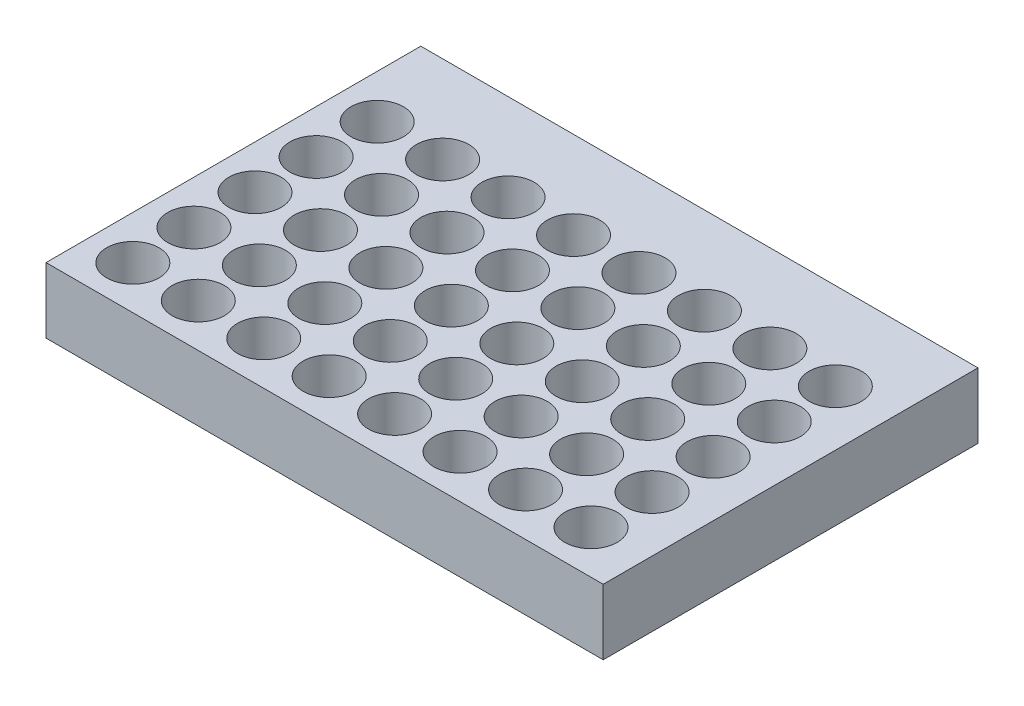
SolidWorks part; units mm, degrees
ref_plane "Front Plane" through (0, 0, 0) normal (0, 0, 1) x (1, 0, 0)
ref_plane "Top Plane" through (0, 0, 0) normal (0, 1, 0) x (1, 0, 0)
ref_plane "Right Plane" through (0, 0, 0) normal (1, 0, 0) x (0, 0, -1)
other "Graphic1"
sketch "Sketch1" plane through (0, 0, 0) normal (0, 1, 0) x (1, 0, 0)
  line L1 (-312.706, 132.0167) -> (-185.006, 132.0167)
  line L2 (-312.706, 132.0167) -> (-312.706, 46.1167)
  line L3 (-312.706, 46.1167) -> (-185.006, 46.1167)
  line L4 (-185.006, 132.0167) -> (-185.006, 46.1167)
  dimension "D1" = 85.9
  dimension "D2" = 127.7
extrude "Boss-Extrude1" add sketch "Sketch1" along normal blind 15
sketch "Sketch2" plane through (0, 15, 0) normal (0, 1, 0) x (1, 0, 0)
  line L0 (-185.006, 132.0167) -> (-312.706, 132.0167) construction
  line L1 (-312.706, 132.0167) -> (-312.706, 46.1167) construction
  circle A0 centre (-302.706, 112.0167) radius 6
  dimension "D1" = 20
  dimension "D3" = 12
  dimension "D2" = 10
extrude "Cut-Extrude1" cut sketch "Sketch2" against normal blind 12 contours A0
pattern_linear "LPattern3" count 8 spacing 15 along (1, 0, 0) count 5 spacing 14 along (0, 0, 1) of "Cut-Extrude1"
sketch "Sketch3" plane through (0, 3, 0) normal (0, 1, 0) x (1, 0, 0)
  circle A0 centre (-302.706, 112.0167) radius 2
extrude "Cut-Extrude2" cut sketch "Sketch3" against normal blind 12
pattern_linear "LPattern4" count 8 spacing 15 along (1, 0, 0) count 5 spacing 14 along (0, 0, 1) of "Cut-Extrude2"
